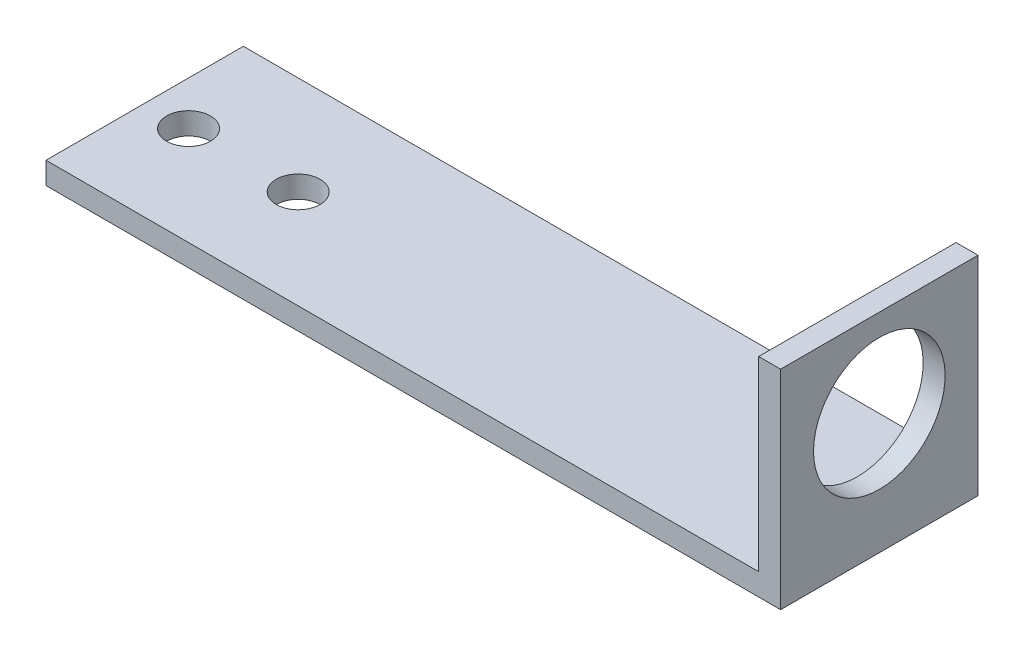
SolidWorks part; units mm, degrees
material "7075-T6 (SN)"
ref_plane "Front Plane" through (0, 0, 0) normal (0, 0, 1) x (1, 0, 0)
ref_plane "Top Plane" through (0, 0, 0) normal (0, 1, 0) x (1, 0, 0)
ref_plane "Right Plane" through (0, 0, 0) normal (1, 0, 0) x (0, 0, -1)
sketch "Sketch1" plane through (0, 0, 0) normal (0, 0, 1) x (1, 0, 0)
  line L0 (0, 0) -> (0, 19)
  line L1 (0, 19) -> (-2, 19)
  line L2 (-2, 19) -> (-2, 2)
  line L3 (-2, 2) -> (-67, 2)
  line L4 (-67, 2) -> (-67, 0)
  line L5 (-67, 0) -> (0, 0)
  dimension "D1" = 19
  dimension "D2" = 67
  dimension "D3" = 2
  dimension "D4" = 2
extrude "Boss-Extrude1" add sketch "Sketch1" along normal blind 18
sketch "Sketch2" plane through (-2, 0, 0) normal (-1, 0, 0) x (0, 0, 1)
  line L0 (9, 20.6644) -> (9, 1.6721) construction
  line L1 (18, 19) -> (0, 19) construction
  circle A0 centre (9, 11) radius 6
  point P7 (9, 19)
  dimension "D1" = 8
  dimension "D2" = 12
extrude "Cut-Extrude1" cut sketch "Sketch2" against normal up to next
sketch "Sketch3" plane through (0, 2, 0) normal (0, 1, 0) x (1, 0, 0)
  line L0 (-73.8781, -9) -> (-39.0393, -9) construction
  line L1 (-67, -18) -> (-67, 0) construction
  circle A0 centre (-63, -9) radius 2
  circle A1 centre (-53, -9) radius 2
  point P4 (-67, -9)
  dimension "D1" = 4
  dimension "D2" = 10
  dimension "D3" = 4
  dimension "D4" = 4
extrude "Cut-Extrude2" cut sketch "Sketch3" against normal up to next
